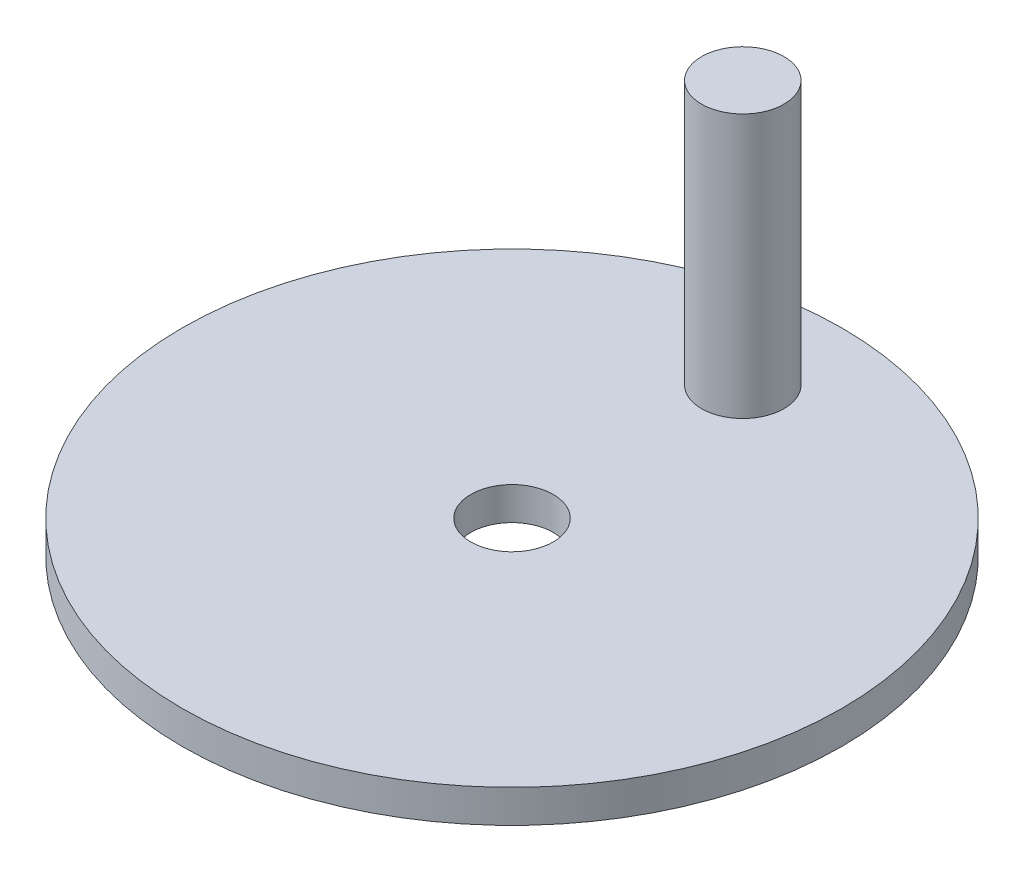
SolidWorks part; units mm, degrees
ref_plane "Front Plane" through (0, 0, 0) normal (0, 0, 1) x (1, 0, 0)
ref_plane "Top Plane" through (0, 0, 0) normal (0, 1, 0) x (1, 0, 0)
ref_plane "Right Plane" through (0, 0, 0) normal (1, 0, 0) x (0, 0, -1)
sketch "Sketch1" plane through (0, 0, 0) normal (0, 1, 0) x (1, 0, 0)
  circle A0 centre (0, 0) radius 25.4
  circle A1 centre (0, 0) radius 3.175
  dimension "D1" = 50.8
  dimension "D2" = 6.35
extrude "Boss-Extrude1" add sketch "Sketch1" along normal blind 2.54
sketch "Sketch2" plane through (0, 2.54, 0) normal (0, 1, 0) x (1, 0, 0)
  line L0 (0, 25.4) -> (0, 0) construction
  circle A0 centre (0, 0) radius 25.4 construction
  circle A1 centre (0, 17.78) radius 3.175
  point P7 (0, 17.7286)
  dimension "D1" = 6.35
  dimension "D2" = 7.62
extrude "Boss-Extrude2" add sketch "Sketch2" along normal blind 20.32
